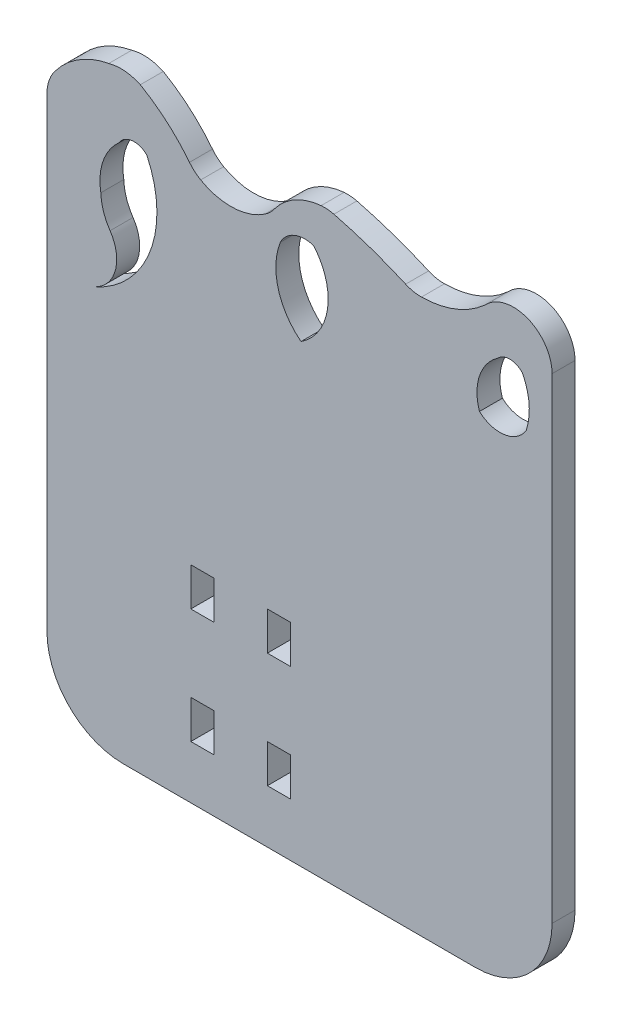
SolidWorks part; units mm, degrees
ref_plane "Alzado" through (0, 0, 0) normal (0, 0, 1) x (1, 0, 0)
ref_plane "Planta" through (0, 0, 0) normal (0, 1, 0) x (1, 0, 0)
ref_plane "Vista lateral" through (0, 0, 0) normal (1, 0, 0) x (0, 0, -1)
sketch "Model" plane through (0, 0, 0) normal (0, 0, 1) x (1, 0, 0)
  line L0 (25.823, 25.3288) -> (25.823, -27.3329)
  line L1 (35.8112, -37.3329) -> (81.8133, -37.3786)
  line L2 (91.823, -27.3786) -> (91.823, 34.8217)
  line L3 (25.823, 33.5065) -> (25.823, 25.3288)
  line L4 (25.7976, -28.8097) -> (25.8007, -23.8097)
  line L5 (54.623, -10.3982) -> (57.623, -10.3982)
  line L6 (54.623, -15.3982) -> (57.623, -15.3982)
  line L7 (44.623, -15.3982) -> (47.623, -15.3982)
  line L8 (44.623, -10.3982) -> (47.623, -10.3982)
  line L9 (57.623, -25.3982) -> (57.623, -30.3982)
  line L10 (47.623, -25.3982) -> (47.623, -30.3982)
  line L11 (57.623, -25.3982) -> (54.623, -25.3982)
  line L12 (57.623, -30.3982) -> (54.623, -30.3982)
  line L13 (47.623, -30.3982) -> (44.623, -30.3982)
  line L14 (47.623, -25.3982) -> (44.623, -25.3982)
  line L15 (44.623, -30.3982) -> (44.623, -25.3982)
  line L16 (54.623, -30.3982) -> (54.623, -25.3982)
  line L17 (44.623, -15.3982) -> (44.623, -10.3982)
  line L18 (54.623, -15.3982) -> (54.623, -10.3982)
  line L19 (47.623, -10.3982) -> (47.623, -15.3982)
  line L20 (57.623, -10.3982) -> (57.623, -15.3982)
  arc A0 (25.823, -27.3329) -> (35.8112, -37.3329) centre (35.823, -27.3329) ccw
  arc A1 (81.8133, -37.3786) -> (91.823, -27.3786) centre (81.823, -27.3786) ccw
  arc A2 (91.823, 34.8217) -> (83.1976, 38.3495) centre (86.7737, 34.7846) ccw
  arc A3 (82.9832, 38.1467) -> (83.1976, 38.3495) centre (79.6566, 41.8796) ccw
  arc A4 (74.7565, 34.9623) -> (82.9832, 38.1467) centre (74.6215, 47.5298) ccw
  arc A5 (72.6888, 35.3856) -> (74.7565, 34.9623) centre (74.7028, 39.962) ccw
  arc A6 (72.6888, 35.3856) -> (63.3161, 38.6163) centre (48.5001, -19.5784) ccw
  arc A7 (63.3161, 38.6163) -> (61.6444, 38.7516) centre (62.0825, 33.7709) ccw
  arc A8 (61.6444, 38.7516) -> (55.5311, 35.304) centre (62.3889, 30.2877) ccw
  arc A9 (54.2821, 34.1045) -> (55.5311, 35.304) centre (51.4955, 38.256) ccw
  arc A10 (45.909, 33.7914) -> (54.2821, 34.1045) centre (49.8423, 40.7191) ccw
  arc A11 (44.4461, 35.0502) -> (45.909, 33.7914) centre (48.3777, 38.1394) ccw
  arc A12 (44.4461, 35.0502) -> (38.0223, 40.6199) centre (26.7922, 21.1784) ccw
  arc A13 (38.0223, 40.6199) -> (33.9035, 40.9683) centre (35.4885, 35.1842) ccw
  arc A14 (33.9035, 40.9683) -> (26.8908, 36.5948) centre (36.0325, 29.7453) ccw
  arc A15 (26.8908, 36.5948) -> (25.823, 33.5065) centre (30.823, 33.5065) ccw
  arc A16 (31.8916, 14.6985) -> (34.0682, 22.1219) centre (29.9395, 19.3017) ccw
  arc A17 (32.8628, 25.8181) -> (34.0682, 22.1219) centre (39.7961, 26.0345) ccw
  arc A18 (35.2544, 32.6843) -> (32.8628, 25.8181) centre (40.1664, 27.1237) ccw
  arc A19 (38.8803, 33.07) -> (35.2544, 32.6843) centre (37.2182, 31.4595) ccw
  arc A20 (31.8916, 14.6985) -> (38.8803, 33.07) centre (26.5744, 27.2363) ccw
  arc A21 (60.6695, 33.7285) -> (56.3084, 31.9361) centre (59.5189, 30.3264) ccw
  arc A22 (56.3084, 31.9361) -> (59.0153, 22.0568) centre (64.3465, 28.828) ccw
  arc A23 (59.0153, 22.0568) -> (60.6695, 33.7285) centre (54.7367, 28.6163) ccw
  arc A24 (87.9749, 32.9313) -> (84.7505, 33.0553) centre (86.3062, 31.5229) ccw
  arc A25 (84.7505, 33.0553) -> (82.3322, 25.8004) centre (88.3787, 27.8154) ccw
  arc A26 (82.3322, 25.8004) -> (88.44, 26.6995) centre (85.0158, 28.7654) ccw
  arc A27 (88.44, 26.6995) -> (87.9749, 32.9313) centre (80.5897, 29.2469) ccw
extrude "Saliente-Extruir1" add sketch "Model" along normal blind 3 contours A14 A15 L3 L0 A0 L1 A1 L2 A2 A3 A4 A5 A6 A7 A8 A9 A10 A11 A12 A13 A27 A26 A25 A24 A23 A22 A21 A20 A16 A17 A18 A19 L5 L20 L6 L18 L8 L19 L7 L17 L12 L16 L11 L9
